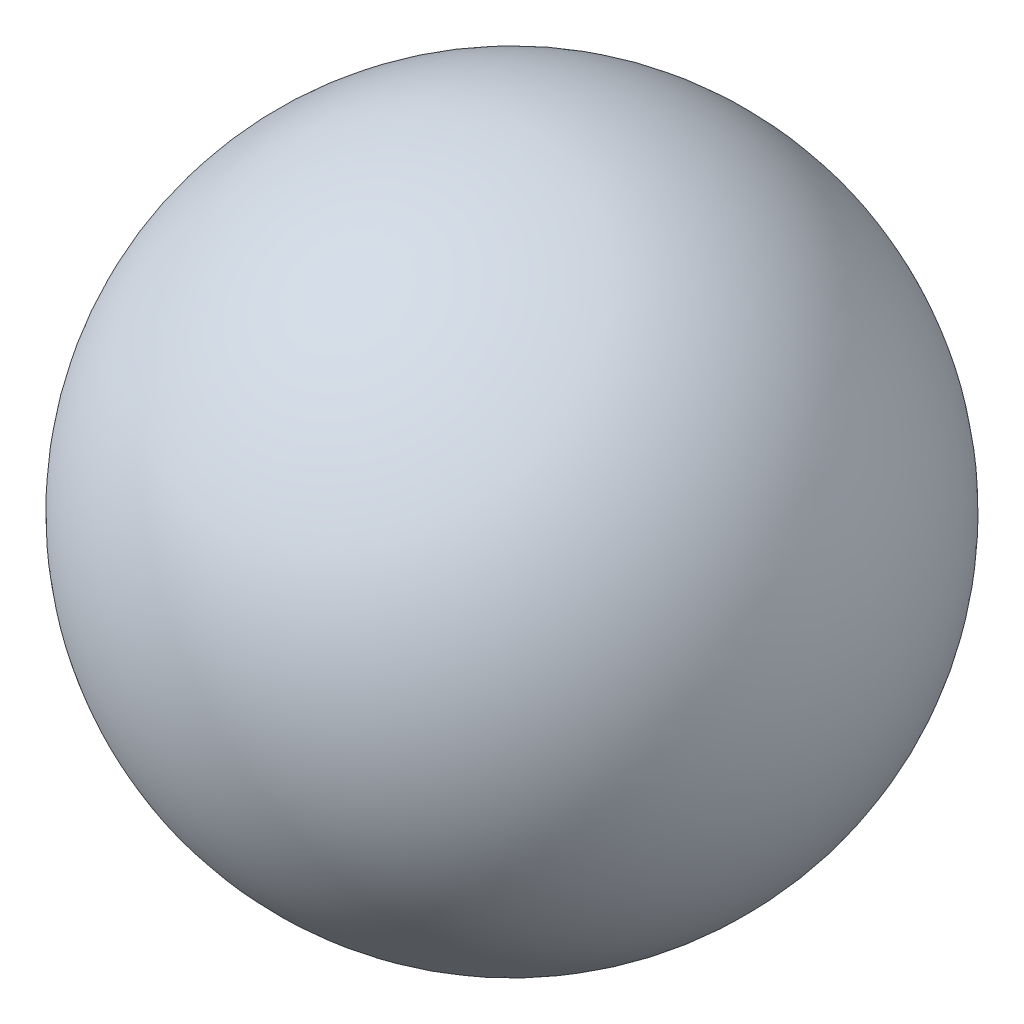
SolidWorks part; units mm, degrees
ref_plane "Front Plane" through (0, 0, 0) normal (0, 0, 1) x (1, 0, 0)
ref_plane "Top Plane" through (0, 0, 0) normal (0, 1, 0) x (1, 0, 0)
ref_plane "Right Plane" through (0, 0, 0) normal (1, 0, 0) x (0, 0, -1)
sketch "Sketch1" plane through (0, 0, 0) normal (0, 1, 0) x (1, 0, 0)
  line L0 (0, 8.2) -> (0, -8.2) construction
  line L1 (0, 8.2) -> (0, -8.2)
  arc A0 (0, -8.2) -> (0, 8.2) centre (0, 0) ccw
  dimension "D1" = 16.4
revolve "Revolve1" add sketch "Sketch1" angle 360 about L0
